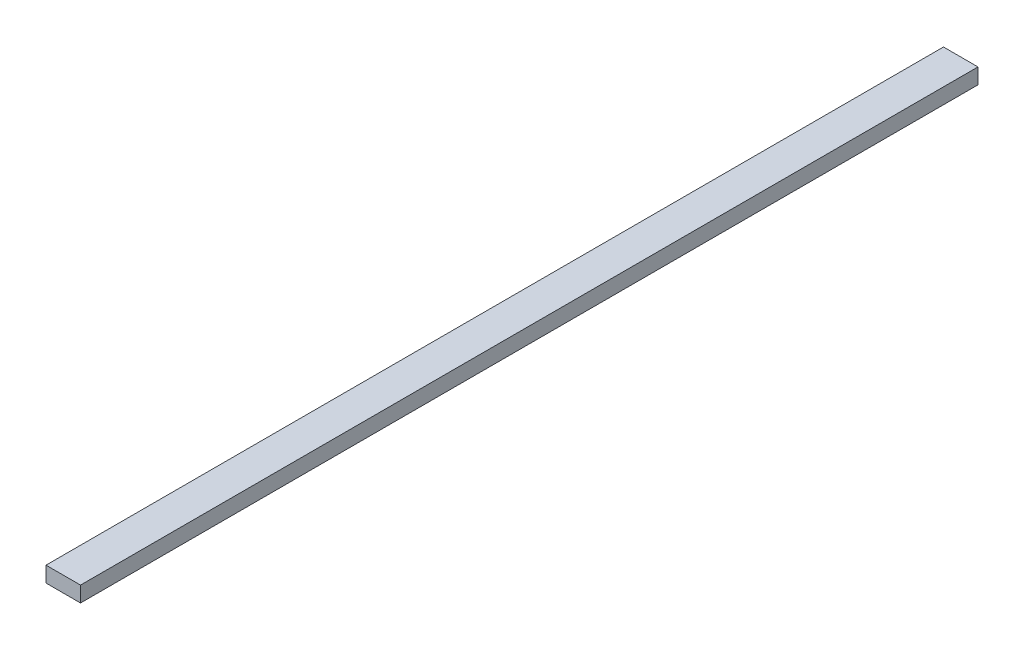
SolidWorks part; units mm, degrees
ref_plane "Alzado" through (0, 0, 0) normal (0, 0, 1) x (1, 0, 0)
ref_plane "Planta" through (0, 0, 0) normal (0, 1, 0) x (1, 0, 0)
ref_plane "Vista lateral" through (0, 0, 0) normal (1, 0, 0) x (0, 0, -1)
sketch "Croquis1" plane through (0, 0, 0) normal (0, 0, 1) x (1, 0, 0)
  line L1 (-10.082, 1.7951) -> (-6.082, 1.7951)
  line L2 (-10.082, 1.7951) -> (-10.082, -0.0049)
  line L3 (-10.082, -0.0049) -> (-6.082, -0.0049)
  line L4 (-6.082, 1.7951) -> (-6.082, -0.0049)
  dimension "D1" = 4
  dimension "D2" = 1.8
extrude "Saliente-Extruir1" add sketch "Croquis1" along normal blind 104
